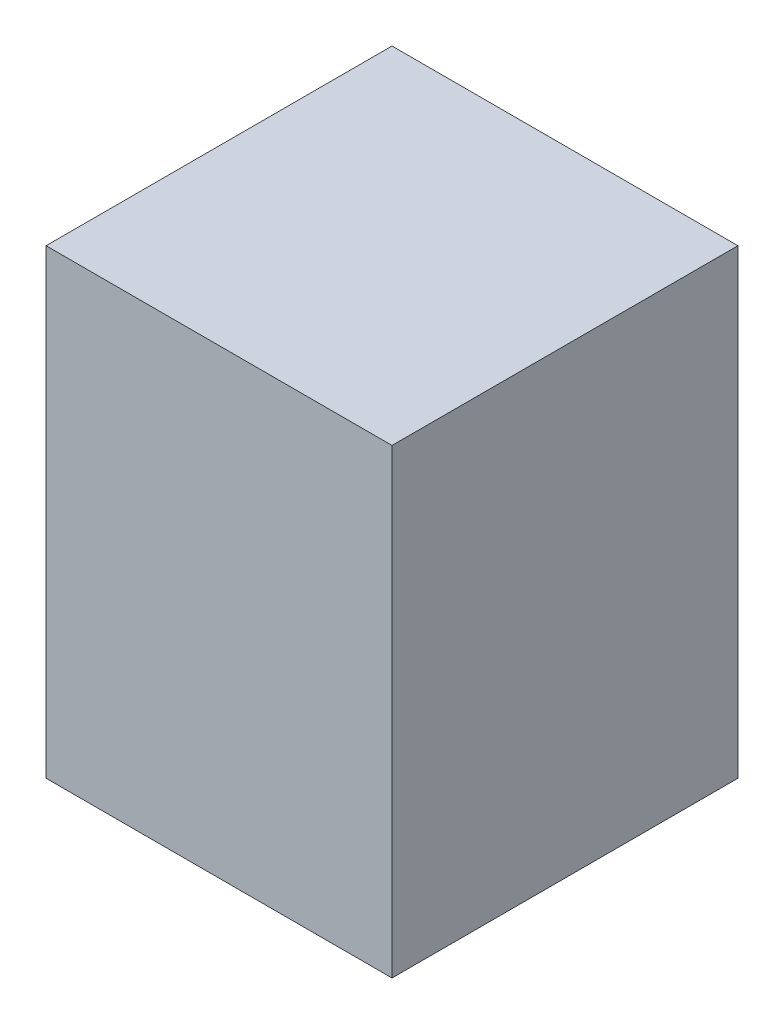
SolidWorks part; units mm, degrees
ref_plane "Alzado" through (0, 0, 0) normal (0, 0, 1) x (1, 0, 0)
ref_plane "Planta" through (0, 0, 0) normal (0, 1, 0) x (1, 0, 0)
ref_plane "Vista lateral" through (0, 0, 0) normal (1, 0, 0) x (0, 0, -1)
sketch "Croquis1" plane through (0, 0, 0) normal (0, 1, 0) x (1, 0, 0)
  line L1 (-15, 15) -> (15, 15)
  line L2 (-15, 15) -> (-15, -15)
  line L3 (-15, -15) -> (15, -15)
  line L4 (15, 15) -> (15, -15)
  line L5 (-15, 15) -> (15, -15) construction
  line L6 (-15, -15) -> (15, 15) construction
  point P0 (0, 0)
  dimension "D1" = 30
  dimension "D2" = 30
extrude "Saliente-Extruir1" add sketch "Croquis1" along normal blind 40
